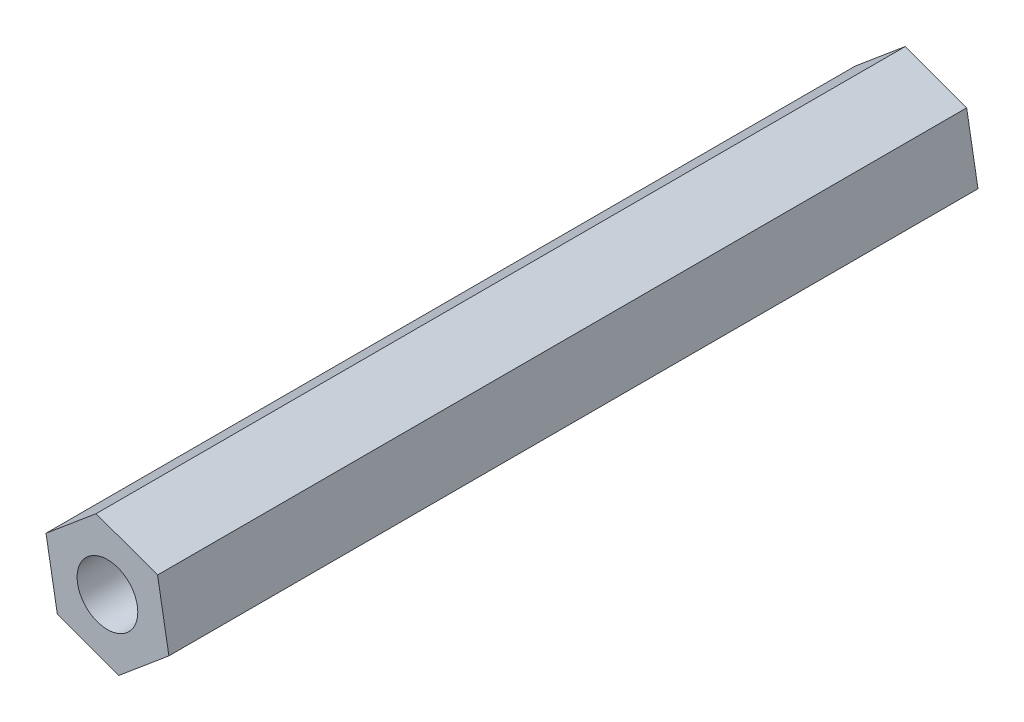
SolidWorks part; units mm, degrees
ref_plane "前视基准面" through (0, 0, 0) normal (0, 0, 1) x (1, 0, 0)
ref_plane "上视基准面" through (0, 0, 0) normal (0, 1, 0) x (1, 0, 0)
ref_plane "右视基准面" through (0, 0, 0) normal (1, 0, 0) x (0, 0, -1)
other "Configuration Table"
sketch "草图1" plane through (0, 0, 0) normal (0, 0, 1) x (1, 0, 0)
  line L1 (-129.7416, -57.0864) -> (-127.2639, -55.0092)
  line L2 (-127.2639, -55.0092) -> (-127.824, -51.825)
  line L3 (-127.824, -51.825) -> (-130.8617, -50.7179)
  line L4 (-130.8617, -50.7179) -> (-133.3394, -52.7951)
  line L5 (-133.3394, -52.7951) -> (-132.7793, -55.9793)
  line L6 (-132.7793, -55.9793) -> (-129.7416, -57.0864)
  circle A0 centre (-130.3017, -53.9021) radius 2.8 construction
  circle A1 centre (-130.3017, -53.9021) radius 1.5
  dimension "D2" = 3
  dimension "D1" = 5.6
extrude "凸台-拉伸1" add sketch "草图1" along normal blind 40
